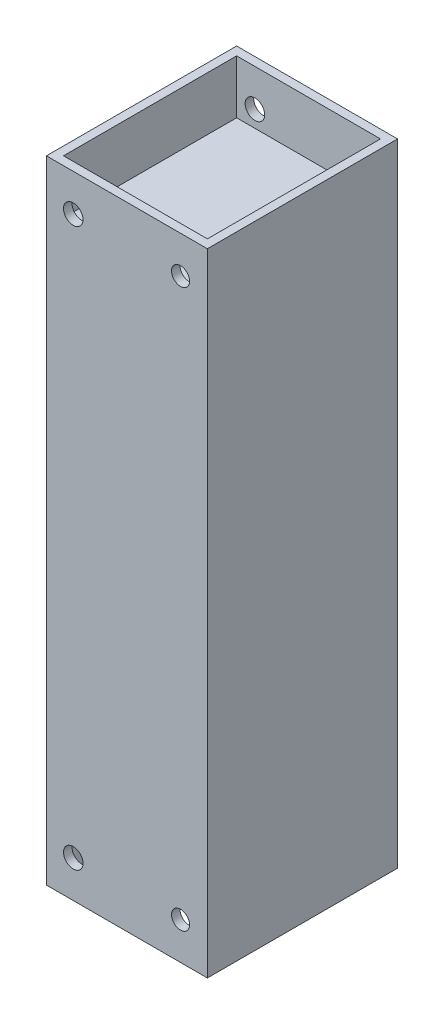
SolidWorks part; units mm, degrees
ref_plane "Front Plane" through (0, 0, 0) normal (0, 0, 1) x (1, 0, 0)
ref_plane "Top Plane" through (0, 0, 0) normal (0, 1, 0) x (1, 0, 0)
ref_plane "Right Plane" through (0, 0, 0) normal (1, 0, 0) x (0, 0, -1)
sketch "Sketch1" plane through (0, 0, 0) normal (0, 1, 0) x (1, 0, 0)
  line L1 (-61.5591, -4.5921) -> (-28.5591, -4.5921)
  line L2 (-61.5591, -4.5921) -> (-61.5591, -43.5921)
  line L3 (-61.5591, -43.5921) -> (-28.5591, -43.5921)
  line L4 (-28.5591, -4.5921) -> (-28.5591, -43.5921)
extrude "Boss-Extrude1" add sketch "Sketch1" along normal blind 13 contours L1 L4 L3 L2
sketch "Sketch2" plane through (0, 13, 0) normal (0, 1, 0) x (1, 0, 0)
  line L1 (-59.8091, -6.3421) -> (-30.3091, -6.3421)
  line L2 (-59.8091, -6.3421) -> (-59.8091, -41.8421)
  line L3 (-59.8091, -41.8421) -> (-30.3091, -41.8421)
  line L4 (-30.3091, -6.3421) -> (-30.3091, -41.8421)
  line L6 (-61.5591, -4.5921) -> (-28.5591, -4.5921) construction
  line L7 (-61.5591, -43.5921) -> (-28.5591, -43.5921) construction
  line L8 (-28.5591, -4.5921) -> (-28.5591, -43.5921) construction
  line L10 (-61.5591, -4.5921) -> (-61.5591, -43.5921) construction
  dimension "D1" = 1.75
  dimension "D2" = 1.75
  dimension "D3" = 1.75
  dimension "D4" = 1.75
extrude "Cut-Extrude1" cut sketch "Sketch2" against normal offset from surface (11 mm away) 2 up to face at (-45.0591, 0, 24.0921)
sketch "Sketch3" plane through (0, 0, 43.5921) normal (0, 0, 1) x (1, 0, 0)
  line L0 (-45.0591, 13) -> (-45.0591, -4.5163) construction
  line L1 (-61.5591, 13) -> (-28.5591, 13) construction
  line L2 (-61.5591, 0) -> (-28.5591, 0) construction
  circle A0 centre (-34.0591, 5.4) radius 1.85
  circle A1 centre (-56.0591, 5.4) radius 2
  dimension "D2" = 11
  dimension "D3" = 5.4
  dimension "D4" = 5.4
  dimension "D1" = 11
extrude "Cut-Extrude2" cut sketch "Sketch3" against normal blind 57
ref_plane "Plane2" through (0, 0, 0) normal (0, -1, 0) x (-1, 0, 0)
sketch "Sketch4" plane through (0, 0, 0) normal (0, -1, 0) x (1, 0, 0)
  line L1 (-61.5591, 4.5921) -> (-28.5591, 4.5921)
  line L2 (-61.5591, 4.5921) -> (-61.5591, 43.5921)
  line L3 (-61.5591, 43.5921) -> (-28.5591, 43.5921)
  line L4 (-28.5591, 4.5921) -> (-28.5591, 43.5921)
extrude "Boss-Extrude2" add sketch "Sketch4" along normal blind 51.75
mirror "Mirror7" about plane through (0, -51.75, 0) normal (0, 1, 0) of bodies 109
